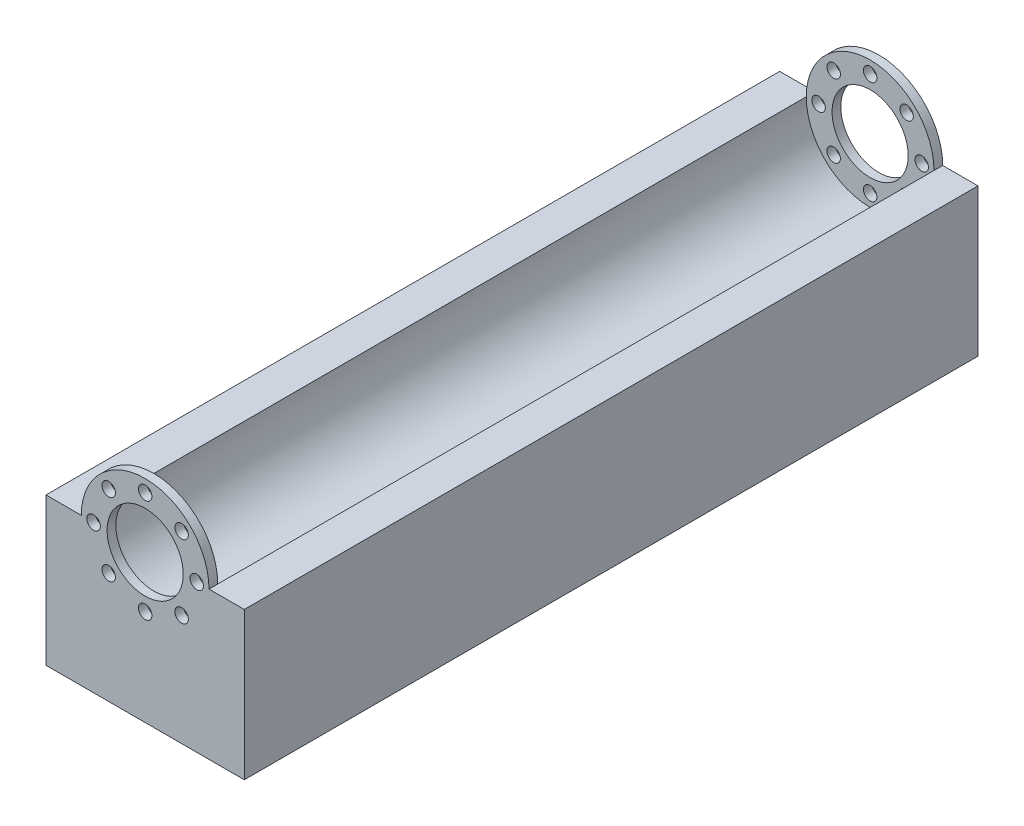
SolidWorks part; units mm, degrees
ref_plane "Plan de face" through (0, 0, 0) normal (0, 0, 1) x (1, 0, 0)
ref_plane "Plan de dessus" through (0, 0, 0) normal (0, 1, 0) x (1, 0, 0)
ref_plane "Plan de droite" through (0, 0, 0) normal (1, 0, 0) x (0, 0, -1)
sketch "Esquisse1" plane through (0, 0, 0) normal (0, 0, 1) x (1, 0, 0)
  line L0 (-25, 0) -> (25, 0) construction
  line L1 (-25, 0) -> (-25, -37.2003)
  line L2 (-25, -37.2003) -> (25, -37.2003)
  line L3 (25, -37.2003) -> (25, 0)
  line L4 (-25, 0) -> (-16.1, 0)
  line L5 (16.1, 0) -> (25, 0)
  circle A0 centre (0, 0) radius 16.1 construction
  arc A1 (-16.1, 0) -> (16.1, 0) centre (0, 0) ccw
  point P6 (0, 0)
  dimension "D1" = 32.2
  dimension "D2" = 50
extrude "Boss.-Extru.1" add sketch "Esquisse1" along normal mid plane 185
sketch "Esquisse2" plane through (0, 0, 92.5) normal (0, 0, 1) x (1, 0, 0)
  line L0 (0, 13) -> (0, 0) construction
  circle A0 centre (0, 0) radius 16.1
  circle A1 centre (0, 13) radius 1.7
  circle A2 centre (0, 0) radius 9.6
  arc A3 (-16.1, 0) -> (16.1, 0) centre (0, 0) ccw construction
  circle A4 centre (9.1924, 9.1924) radius 1.7
  circle A5 centre (13, 0) radius 1.7
  circle A6 centre (9.1924, -9.1924) radius 1.7
  circle A7 centre (0, -13) radius 1.7
  circle A8 centre (-9.1924, -9.1924) radius 1.7
  circle A9 centre (-13, 0) radius 1.7
  circle A10 centre (-9.1924, 9.1924) radius 1.7
  dimension "D1" = 19.2
  dimension "D2" = 3.4
  dimension "D3" = 13
  dimension "D4" = 8
extrude "Boss.-Extru.2" add sketch "Esquisse2" against normal blind 2.2
mirror "Symétrie1" about plane through (0, 0, 0) normal (0, 0, 1) of "Boss.-Extru.2"
